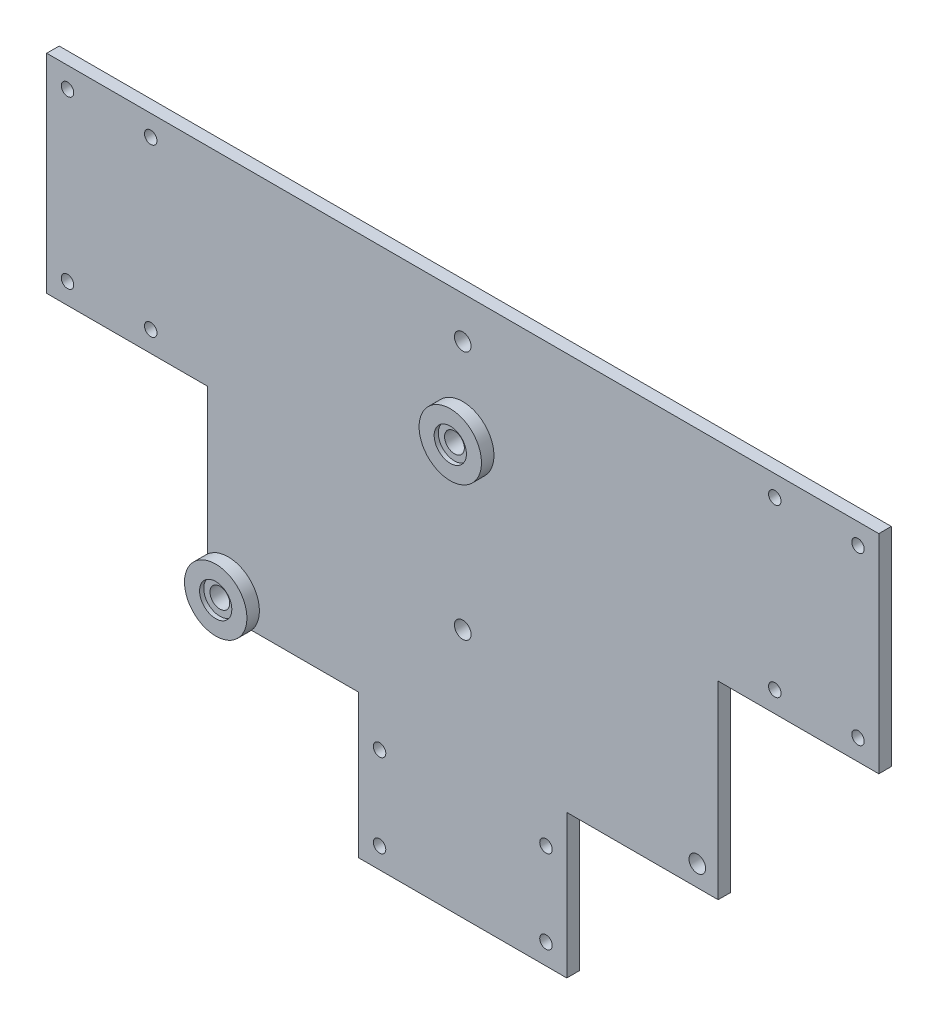
SolidWorks part; units mm, degrees
ref_plane "Plan de face" through (0, 0, 0) normal (0, 0, 1) x (1, 0, 0)
ref_plane "Plan de dessus" through (0, 0, 0) normal (0, 1, 0) x (1, 0, 0)
ref_plane "Plan de droite" through (0, 0, 0) normal (1, 0, 0) x (0, 0, -1)
sketch "Esquisse1" plane through (0, 0, 0) normal (0, 0, 1) x (1, 0, 0)
  line L0 (-25, 0) -> (25, 0) construction
  line L1 (0, 50) -> (-100, 50)
  line L2 (25, -80) -> (25, -45.5212)
  line L3 (-70, 50) -> (-70, 0) construction
  line L4 (25, -80) -> (-25, -80)
  line L5 (-25, -50) -> (25, -50) construction
  line L6 (-25, -65) -> (25, -65) construction
  line L7 (-25, -80) -> (-25, -45.5212)
  line L8 (0, 50) -> (0, -80) construction
  line L9 (-85, 50) -> (-85, 0) construction
  line L10 (0, 50) -> (100, 50)
  line L11 (100, 50) -> (100, 0)
  line L12 (100, 0) -> (61.3816, 0)
  line L13 (-100, 50) -> (-100, 0)
  line L14 (-100, 0) -> (-61.3816, 0)
  line L15 (61.3816, 0) -> (25, 0) construction
  line L16 (-100, 25) -> (-70, 25) construction
  line L17 (-25, -45.5212) -> (-25, 0) construction
  line L18 (-61.3816, 0) -> (-61.3816, -45.5212)
  line L19 (-61.3816, -45.5212) -> (-25, -45.5212)
  line L20 (0, -20) -> (-25, -20) construction
  line L21 (25, -45.5212) -> (25, 0) construction
  line L22 (61.3816, 0) -> (61.3816, -45.5212)
  line L23 (61.3816, -45.5212) -> (25, -45.5212)
  line L24 (0, -20) -> (-56.3816, -40.5212) construction
  circle A0 centre (0, 20) radius 2
  circle A1 centre (0, -20) radius 2
  circle A2 centre (0, 40) radius 2
  circle A3 centre (-20, -55) radius 1.5
  circle A4 centre (20, -55) radius 1.5
  circle A5 centre (20, -75) radius 1.5
  circle A6 centre (-20, -75) radius 1.5
  circle A7 centre (-95, 45) radius 1.5
  circle A8 centre (-75, 45) radius 1.5
  circle A9 centre (-75, 5) radius 1.5
  circle A10 centre (-95, 5) radius 1.5
  circle A11 centre (75, 5) radius 1.5
  circle A12 centre (95, 5) radius 1.5
  circle A13 centre (75, 45) radius 1.5
  circle A14 centre (95, 45) radius 1.5
  circle A15 centre (56.3816, -40.5212) radius 2
  circle A17 centre (-56.3816, -40.5212) radius 2
  point P0 (0, 0)
  point P2 (0, 0)
  dimension "D3" = 4
  dimension "D4" = 4
  dimension "D5" = 20
  dimension "D7" = 4
  dimension "D13" = 3
  dimension "D14" = 20
  dimension "D19" = 3
  dimension "D20" = 10
  dimension "D21" = 20
  dimension "D22" = 5
  dimension "D23" = 5
  dimension "D24" = 60
  dimension "D25" = 20
  dimension "D26" = 4
  dimension "D27" = 25
  dimension "D6" = 20
  dimension "D8" = 40
  dimension "D9" = 80
  dimension "D10" = 30
  dimension "D11" = 30
  dimension "D12" = 15
  dimension "D15" = 10
  dimension "D16" = 100
  dimension "D17" = 50
  dimension "D18" = 15
extrude "Boss.-Extru.1" add sketch "Esquisse1" along normal blind 3
sketch "Esquisse3" plane through (0, 0, 0) normal (0, 0, -1) x (-1, 0, 0)
  circle A0 centre (0, 20) radius 7.5
  circle A1 centre (56.3816, -40.5212) radius 7.5
  dimension "D1" = 15
  dimension "D2" = 15
extrude "Boss.-Extru.2" add sketch "Esquisse3" against normal blind 6
sketch "Esquisse4" plane through (0, 0, 6) normal (0, 0, 1) x (1, 0, 0)
  circle A0 centre (-56.3816, -40.5212) radius 3.875
  circle A1 centre (0, 20) radius 3.875
  dimension "D1" = 7.75
  dimension "D2" = 7.75
extrude "Enlèv. mat.-Extru.1" cut sketch "Esquisse4" against normal blind 1
sketch "Esquisse5" plane through (0, 0, 5) normal (0, 0, 1) x (1, 0, 0)
  circle A0 centre (-56.3816, -40.5212) radius 2.375
  circle A1 centre (0, 20) radius 2.375
  dimension "D1" = 4.75
  dimension "D2" = 4.75
extrude "Enlèv. mat.-Extru.2" cut sketch "Esquisse5" against normal blind 4
